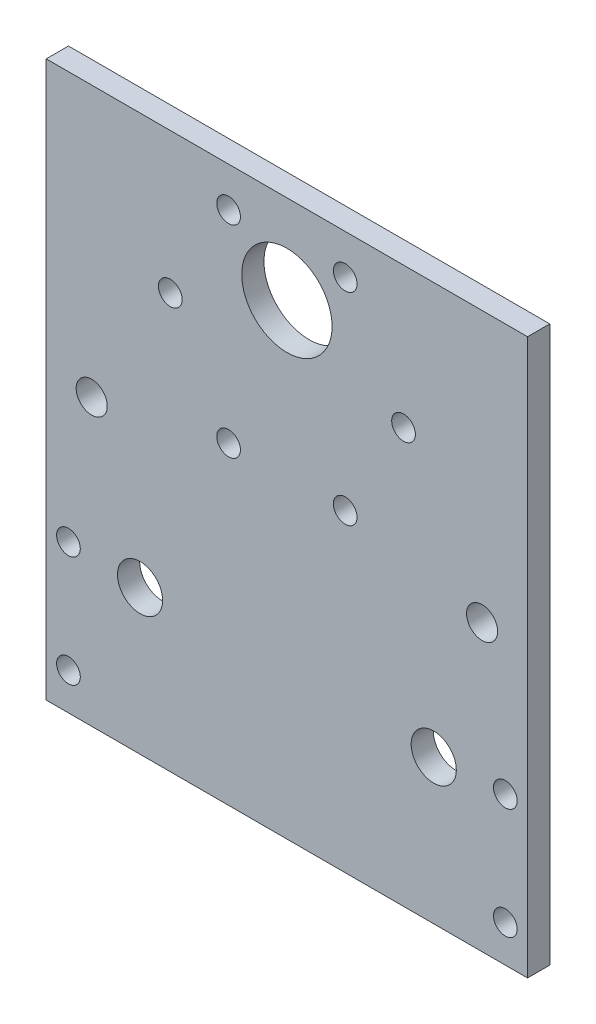
SolidWorks part; units mm, degrees
ref_plane "正面" through (0, 0, 0) normal (0, 0, 1) x (1, 0, 0)
ref_plane "平面" through (0, 0, 0) normal (0, 1, 0) x (1, 0, 0)
ref_plane "右側面" through (0, 0, 0) normal (1, 0, 0) x (0, 0, -1)
sketch "ｽｹｯﾁ1" plane through (0, 0, 0) normal (0, 0, 1) x (1, 0, 0)
  line L0 (0, 0) -> (0, 7)
  line L1 (-32.5, 12.5) -> (32.5, 12.5)
  line L2 (-32.5, 12.5) -> (-32.5, -12.5)
  line L3 (-32.5, -12.5) -> (32.5, -12.5)
  line L4 (32.5, 12.5) -> (32.5, -12.5)
  line L5 (-32.5, 12.5) -> (32.5, -12.5) construction
  line L6 (-32.5, -12.5) -> (32.5, 12.5) construction
  line L7 (0, 7) -> (19.83, 7)
  line L8 (0, 7) -> (-19.83, 7)
  circle A0 centre (-19.83, 7) radius 3.05
  circle A1 centre (19.83, 7) radius 3.05
  point P0 (0, 0)
  dimension "D3" = 6.1
  dimension "D4" = 6.1
  dimension "D1" = 19.83
  dimension "D2" = 19.83
  dimension "D5" = 25
  dimension "D6" = 65
  dimension "D7" = 7
extrude "ﾎﾞｽ - 押し出し1" add sketch "ｽｹｯﾁ1" along normal blind 3
sketch "ｽｹｯﾁ2" plane through (0, 0, 3) normal (0, 0, 1) x (1, 0, 0)
  line L0 (-32.5, 12.5) -> (-32.5, -12.5) construction
  line L1 (-32.5, 12.5) -> (-29.5, 12.5)
  line L2 (-32.5, 12.5) -> (-32.5, 7.5)
  line L3 (-32.5, 7.5) -> (-29.5, 7.5)
  line L4 (-29.5, 12.5) -> (-29.5, 7.5)
  line L5 (-32.5, -12.5) -> (-29.5, -12.5)
  line L6 (-32.5, -12.5) -> (-32.5, -7.5)
  line L7 (-32.5, -7.5) -> (-29.5, -7.5)
  line L8 (-29.5, -12.5) -> (-29.5, -7.5)
  line L9 (-32.5, -12.5) -> (32.5, -12.5) construction
  line L10 (32.5, 12.5) -> (32.5, -12.5) construction
  line L11 (32.5, -12.5) -> (29.5, -12.5)
  line L12 (32.5, -12.5) -> (32.5, -7.5)
  line L13 (32.5, -7.5) -> (29.5, -7.5)
  line L14 (29.5, -12.5) -> (29.5, -7.5)
  line L16 (32.5, 12.5) -> (29.5, 12.5)
  line L17 (32.5, 12.5) -> (32.5, 7.5)
  line L18 (32.5, 7.5) -> (29.5, 7.5)
  line L19 (29.5, 12.5) -> (29.5, 7.5)
  circle A0 centre (-29.5, 7.5) radius 1.6
  circle A1 centre (-29.5, -7.5) radius 1.6
  circle A2 centre (29.5, 7.5) radius 1.6
  circle A3 centre (29.5, -7.5) radius 1.6
  dimension "D9" = 3.2
  dimension "D10" = 3.2
  dimension "D11" = 3.2
  dimension "D12" = 3.2
  dimension "D1" = 3
  dimension "D2" = 5
  dimension "D3" = 3
  dimension "D4" = 5
  dimension "D5" = 3
  dimension "D6" = 5
  dimension "D7" = 3
  dimension "D8" = 5
extrude "ｶｯﾄ - 押し出し1" cut sketch "ｽｹｯﾁ2" against normal through all contours L3 A0 L4 | L4 A0 L3 | L7 A1 L8 | L8 A1 L7 | L18 A2 L19 | L19 A2 L18 | L14 A3 L13 | L13 A3 L14
sketch "ｽｹｯﾁ3" plane through (0, 12.5, 0) normal (0, 1, 0) x (1, 0, 0)
  line L0 (-32.5, 0) -> (32.5, 0) construction
  line L1 (-32.5, -3) -> (32.5, -3)
  line L2 (-32.5, -3) -> (-32.5, 0)
  line L3 (-32.5, 0) -> (32.5, 0)
  line L4 (32.5, -3) -> (32.5, 0)
  line L5 (32.5, -3) -> (32.5, 0) construction
extrude "ﾎﾞｽ - 押し出し2" add sketch "ｽｹｯﾁ3" along normal blind 50
sketch "ｽｹｯﾁ4" plane through (0, 0, 0) normal (0, 0, 1) x (1, 0, 0)
  line L0 (0, 62.5) -> (0, 43.5)
  line L1 (-32.5, 62.5) -> (32.5, 62.5) construction
  line L2 (0, 43.5) -> (7.875, 57.1399)
  line L3 (0, 43.5) -> (15.75, 43.5)
  line L4 (0, 43.5) -> (7.875, 29.8601)
  line L5 (0, 43.5) -> (-7.875, 29.8601)
  line L6 (0, 43.5) -> (-15.75, 43.5)
  line L7 (0, 43.5) -> (-7.875, 57.1399)
  line L8 (0, 43.5) -> (0, 50.5)
  circle A0 centre (0, 43.5) radius 15.75
  circle A1 centre (-7.875, 57.1399) radius 1.6
  circle A2 centre (7.875, 57.1399) radius 1.6
  circle A3 centre (15.75, 43.5) radius 1.6
  circle A4 centre (7.875, 29.8601) radius 1.6
  circle A5 centre (-7.875, 29.8601) radius 1.6
  circle A6 centre (-15.75, 43.5) radius 1.6
  circle A7 centre (0, 50.5) radius 6.1
  dimension "D1" = 31.5
  dimension "D8" = 3.2
  dimension "D9" = 3.2
  dimension "D10" = 3.2
  dimension "D11" = 3.2
  dimension "D12" = 3.2
  dimension "D13" = 3.2
  dimension "D15" = 12.2
  dimension "D2" = 19
  dimension "D3" = 30
  dimension "D4" = 60
  dimension "D5" = 60
  dimension "D6" = 60
  dimension "D7" = 30
  dimension "D14" = 7
extrude "ｶｯﾄ - 押し出し4" cut sketch "ｽｹｯﾁ4" along normal blind 40 contours A0 A2 | A0 A2 L2 | L2 A2 A0 | A0 A3 | A0 A3 L3 | L2 A7 L0 | L0 A7 L7 | L2 A7 | L7 A7 | A0 A1 | L7 A1 A0 | A0 A1 L7 | A0 A6 | L6 A6 A0 | A0 A6 L6 | A0 A4 | A0 A4 L4 | A0 A5 L5 | L5 A5 A0 | A0 A5 | L3 A3 A0
sketch "ｽｹｯﾁ5" plane through (0, 0, 0) normal (0, 0, -1) x (-1, 0, 0)
  circle A0 centre (-26.3609, 26) radius 2.1
  dimension "D1" = 4.2
extrude "ｶｯﾄ - 押し出し5" cut sketch "ｽｹｯﾁ5" against normal blind 10
sketch "ｽｹｯﾁ6" plane through (0, 0, 3) normal (0, 0, 1) x (1, 0, 0)
  line L1 (26.3609, 26) -> (32.5, 26)
  line L2 (32.5, 62.5) -> (32.5, -12.5) construction
  line L3 (32.5, 26) -> (32.5, -12.5)
  line L4 (-32.5, -12.5) -> (-32.5, 26)
  line L5 (-32.5, 62.5) -> (-32.5, -12.5) construction
  line L6 (-32.5, 26) -> (-26.36, 26)
  circle A0 centre (-26.36, 26) radius 2.1
  dimension "D5" = 4.2
  dimension "D1" = 38.5
  dimension "D2" = 6.1391
  dimension "D3" = 38.5
  dimension "D4" = 6.14
extrude "ｶｯﾄ - 押し出し6" cut sketch "ｽｹｯﾁ6" against normal blind 10
